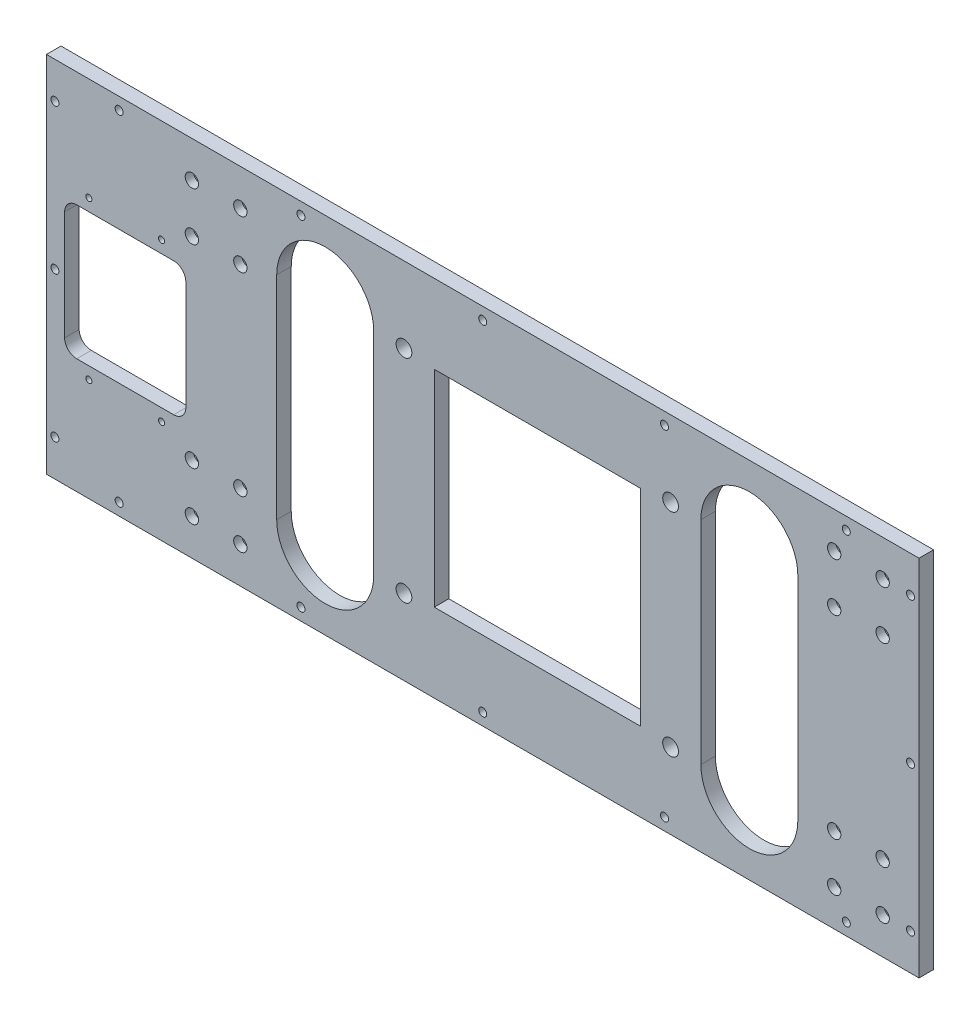
SolidWorks part; units mm, degrees
material "A3钢"
ref_plane "前视基准面" through (0, 0, 0) normal (0, 0, 1) x (1, 0, 0)
ref_plane "上视基准面" through (0, 0, 0) normal (0, 1, 0) x (1, 0, 0)
ref_plane "右视基准面" through (0, 0, 0) normal (1, 0, 0) x (0, 0, -1)
sketch "草图1" plane through (0, 0, 0) normal (0, 0, 1) x (1, 0, 0)
  line L1 (-360, -150) -> (360, -150)
  line L2 (-360, -150) -> (-360, 150)
  line L3 (-360, 150) -> (360, 150)
  line L4 (360, -150) -> (360, 150)
  line L5 (-360, -150) -> (360, 150) construction
  line L6 (-360, 150) -> (360, -150) construction
  point P0 (0, 0)
  dimension "D1" = 720
  dimension "D2" = 300
extrude "凸台-拉伸1" add sketch "草图1" along normal mid plane 12
sketch "草图2" plane through (0, 0, 6) normal (0, 0, 1) x (1, 0, 0)
  line L0 (45, 0) -> (235.2382, 0) construction
  line L1 (360, 150) -> (-360, 150) construction
  line L2 (-360, -150) -> (360, -150) construction
  line L3 (360, -150) -> (360, 150) construction
  circle A0 centre (45, 0) radius 30
  dimension "D1" = 60
  dimension "D2" = 315
extrude "切除-拉伸1" cut sketch "草图2" against normal through all
sketch "草图5" plane through (0, 0, 6) normal (0, 0, 1) x (1, 0, 0)
  line L0 (-45, 0) -> (45, 0) construction
  line L1 (45, 34.9467) -> (45, 0) construction
  circle A0 centre (-130, 87.5) radius 22.5
  circle A1 centre (-130, -87.5) radius 22.5
  circle A2 centre (220, -87.5) radius 22.5
  circle A3 centre (220, 87.5) radius 22.5
  dimension "D1" = 350
  dimension "D2" = 175
  dimension "D3" = 45
extrude "切除-拉伸2" cut sketch "草图5" against normal through all
hole_wizard "M6 螺纹孔1" positions "草图6" profile "草图7" tap size "M6" standard "GB" end condition through all
sketch "草图6" plane through (0, 0, 6) normal (0, 0, 1) x (1, 0, 0)
  line L0 (-243.226, 0) -> (45, 0) construction
  line L3 (45, 139.8405) -> (45, 0) construction
  line L4 (-130, 87.5) -> (-229.3436, 87.5) construction
  line L7 (-130, 87.5) -> (-130, 125.6853) construction
  circle A0 centre (45, 0) radius 30 construction
  point P117 (-154.5, 105)
  point P132 (-105.5, 105)
  point P133 (-105.5, 70)
  point P134 (-154.5, 70)
  point P135 (244.5, 70)
  point P136 (195.5, 70)
  point P137 (195.5, 105)
  point P138 (244.5, 105)
  point P139 (244.5, -105)
  point P140 (195.5, -105)
  point P141 (195.5, -70)
  point P142 (244.5, -70)
  point P143 (-154.5, -70)
  point P144 (-105.5, -70)
  point P145 (-105.5, -105)
  point P146 (-154.5, -105)
  dimension "D1" = 49
  dimension "D2" = 35
sketch "草图7" plane through (-154.5, -105, 6) normal (1, 0, 0) x (0, -1, 0)
  line L0 (0, 0) -> (0, 12)
  line L1 (0, 12) -> (2.5, 12)
  line L2 (2.5, 12) -> (2.5, 0)
  line L5 (2.5, 0) -> (0, 0)
  line L11 (0, -6.35) -> (0, 107.95) construction
  dimension "通孔螺纹孔钻头直径" = 5
  dimension "通孔螺纹孔钻头深度" = 12
cosmetic thread "孔螺蚊线1" parameters "D2"=6
cosmetic thread "孔螺蚊线2" parameters "D2"=6
cosmetic thread "孔螺蚊线3" parameters "D2"=6
cosmetic thread "孔螺蚊线4" parameters "D2"=6
cosmetic thread "孔螺蚊线5" parameters "D2"=6
cosmetic thread "孔螺蚊线6" parameters "D2"=6
cosmetic thread "孔螺蚊线7" parameters "D2"=6
cosmetic thread "孔螺蚊线8" parameters "D2"=6
cosmetic thread "孔螺蚊线9" parameters "D2"=6
cosmetic thread "孔螺蚊线10" parameters "D2"=6
cosmetic thread "孔螺蚊线11" parameters "D2"=6
cosmetic thread "孔螺蚊线12" parameters "D2"=6
cosmetic thread "孔螺蚊线13" parameters "D2"=6
cosmetic thread "孔螺蚊线14" parameters "D2"=6
cosmetic thread "孔螺蚊线15" parameters "D2"=6
cosmetic thread "孔螺蚊线16" parameters "D2"=6
hole_wizard "Ø13.0 (13) 直径孔1" positions "草图15" profile "草图16" hole size "Ø13.0" standard "GB" end condition through all
sketch "草图15" plane through (0, 0, 6) normal (0, 0, 1) x (1, 0, 0)
  line L0 (-244.6825, 0) -> (45, 0) construction
  line L3 (45, 139.2576) -> (45, -142.8825) construction
  circle A0 centre (45, 0) radius 30 construction
  point P0 (-65, 87.5)
  point P15 (155, 87.5)
  point P16 (155, -87.5)
  point P17 (-65, -87.5)
  dimension "D1" = 220
  dimension "D2" = 175
sketch "草图16" plane through (-65, 87.5, 6) normal (1, 0, 0) x (0, -1, 0)
  line L0 (0, 0) -> (0, 12)
  line L1 (0, 12) -> (6.5, 12)
  line L2 (6.5, 12) -> (6.5, 0)
  line L5 (6.5, 0) -> (0, 0)
  line L11 (0, -6.35) -> (0, 107.95) construction
  dimension "通孔孔直径" = 13
  dimension "通孔孔深度" = 12
sketch "草图17" plane through (0, 0, 6) normal (0, 0, 1) x (1, 0, 0)
  line L0 (-152.5, 87.5) -> (-107.5, 87.5) construction
  line L2 (225, -87.5) -> (-225, -87.5)
  line L3 (225, -87.5) -> (225, 87.5)
  line L4 (225, 87.5) -> (-225, 87.5)
  line L5 (-225, -87.5) -> (-225, 87.5)
  line L6 (225, -87.5) -> (-225, 87.5) construction
  line L7 (225, 87.5) -> (-225, -87.5) construction
  line L8 (-241, 102.5) -> (-209, 102.5)
  line L9 (-241, 102.5) -> (-241, 72.5)
  line L10 (-241, 72.5) -> (-209, 72.5)
  line L11 (-209, 102.5) -> (-209, 72.5)
  line L12 (-241, 102.5) -> (-209, 72.5) construction
  line L13 (-241, 72.5) -> (-209, 102.5) construction
  circle A0 centre (-130, 87.5) radius 22.5 construction
  point P5 (0, 0)
  dimension "D1" = 32
  dimension "D2" = 30
  dimension "D3" = 450
ref_plane "基准面1" through (0, 0, 0) normal (0, -1, 0) x (-1, 0, 0)
ref_plane "基准面2" through (0, 0, 0) normal (-1, 0, 0) x (0, 0, 1)
sketch "草图18" plane through (0, 0, 6) normal (0, 0, 1) x (1, 0, 0)
  line L0 (45, 0) -> (606.8786, 0) construction
  line L1 (310, -100) -> (-220, -100)
  line L2 (310, -100) -> (310, 100)
  line L3 (310, 100) -> (-220, 100)
  line L4 (-220, -100) -> (-220, 100)
  line L5 (310, -100) -> (-220, 100) construction
  line L6 (310, 100) -> (-220, -100) construction
  line L7 (45, 0) -> (45, 422.5031) construction
  line L8 (330, -80) -> (290, -120) construction
  line L9 (-240, 120) -> (-200, 120)
  line L10 (-240, 120) -> (-240, 80)
  line L11 (-240, 80) -> (-200, 80)
  line L12 (-200, 120) -> (-200, 80)
  line L13 (-240, 120) -> (-200, 80) construction
  line L14 (-240, 80) -> (-200, 120) construction
  line L15 (-240, -120) -> (-200, -120)
  line L16 (-240, -120) -> (-240, -80)
  line L17 (-240, -80) -> (-200, -80)
  line L18 (-200, -120) -> (-200, -80)
  line L19 (-240, -120) -> (-200, -80) construction
  line L20 (-240, -80) -> (-200, -120) construction
  line L21 (330, -120) -> (290, -80) construction
  line L22 (330, 80) -> (290, 120) construction
  line L23 (330, 120) -> (290, 80) construction
  line L24 (290, -120) -> (290, -80)
  line L25 (330, -80) -> (290, -80)
  line L26 (330, -120) -> (330, -80)
  line L27 (330, -120) -> (290, -120)
  line L28 (290, 120) -> (290, 80)
  line L29 (330, 80) -> (290, 80)
  line L30 (330, 120) -> (330, 80)
  line L31 (330, 120) -> (290, 120)
  line L32 (310, -100) -> (310, 100)
  line L33 (360, -150) -> (360, 150) construction
  line L34 (360, 150) -> (-360, 150) construction
  line L35 (-360, -150) -> (360, -150) construction
  dimension "D1" = 530
  dimension "D2" = 200
  dimension "D3" = 40
  dimension "D4" = 40
  dimension "D5" = 50
hole_wizard "打孔尺寸(%根据)内六角圆柱头螺钉的类型4" positions "3D草图1" profile "草图20" counterbore size "M6" standard "GB" end condition through all
sketch3d "3D草图1"
  point P0 (-240, 120, 6)
  point P3 (-200, 120, 6)
  point P6 (-200, 80, 6)
  point P9 (-240, 80, 6)
  point P12 (-200, -80, 6)
  point P15 (-200, -120, 6)
  point P18 (-240, -120, 6)
  point P21 (-240, -80, 6)
  point P25 (290, 120, 6)
  point P28 (330, 120, 6)
  point P31 (330, 80, 6)
  point P34 (290, 80, 6)
  point P37 (290, -80, 6)
  point P40 (330, -80, 6)
  point P43 (330, -120, 6)
  point P46 (290, -120, 6)
sketch "草图20" plane through (-240, 120, 6) normal (1, 0, 0) x (0, -1, 0)
  line L0 (0, 0) -> (0, 12)
  line L1 (0, 12) -> (3.3, 12)
  line L3 (3.3, 12) -> (3.3, 6.8)
  line L4 (3.3, 6.8) -> (5.5, 6.8)
  line L5 (5.5, 6.8) -> (5.5, 0)
  line L7 (5.5, 0) -> (0, 0)
  line L11 (0, -6.35) -> (0, 107.95) construction
  dimension "通孔孔直径" = 6.6
  dimension "通孔孔深度" = 12
  dimension "柱形沉头孔直径" = 11
  dimension "柱形沉头孔深度" = 6.8
sketch "草图21" plane through (0, 0, 6) normal (0, 0, 1) x (1, 0, 0)
  line L1 (-30, -75) -> (120, -75)
  line L2 (-30, -75) -> (-30, 75)
  line L3 (-30, 75) -> (120, 75)
  line L4 (120, -75) -> (120, 75)
  line L5 (-30, -75) -> (120, 75) construction
  line L6 (-30, 75) -> (120, -75) construction
  point P0 (45, 0)
  dimension "D1" = 150
sketch "草图22" plane through (0, 0, 6) normal (0, 0, 1) x (1, 0, 0)
  line L1 (-336.75, -24.75) -> (-287.25, -24.75)
  line L2 (-336.75, -24.75) -> (-336.75, 24.75)
  line L3 (-336.75, 24.75) -> (-287.25, 24.75)
  line L4 (-287.25, -24.75) -> (-287.25, 24.75)
  line L5 (-336.75, -24.75) -> (-287.25, 24.75) construction
  line L6 (-336.75, 24.75) -> (-287.25, -24.75) construction
  line L7 (0, 0) -> (-421.3567, 0) construction
  circle A1 centre (-240, 80) radius 3.3 construction
  point P0 (-312, 0)
  dimension "D1" = 72
  dimension "D2" = 49.5
  dimension "D3" = 49.5
sketch "草图26" plane through (0, 0, 6) normal (0, 0, 1) x (1, 0, 0)
  line L0 (45, 0) -> (485.4738, 0) construction
  line L1 (0.5, -44.5) -> (89.5, -44.5)
  line L2 (0.5, -44.5) -> (0.5, 44.5)
  line L3 (0.5, 44.5) -> (89.5, 44.5)
  line L4 (89.5, -44.5) -> (89.5, 44.5)
  line L5 (0.5, -44.5) -> (89.5, 44.5) construction
  line L6 (0.5, 44.5) -> (89.5, -44.5) construction
  line L7 (45, 0) -> (45, 266.8061) construction
  dimension "D1" = 89
  dimension "D2" = 89
hole_wizard "Ø11.0 (11) 直径孔1" positions "3D草图3" profile "草图27" hole size "Ø11.0" standard "GB" end condition through all
sketch3d "3D草图3"
  point P0 (-30, 75, 6)
  point P3 (122.598, 78.1933, 6)
  point P6 (-30, -75, 6)
  point P9 (120, -75, 6)
sketch "草图27" plane through (-30, 75, 6) normal (1, 0, 0) x (0, -1, 0)
  line L0 (0, 0) -> (0, 12)
  line L1 (0, 12) -> (5.5, 12)
  line L2 (5.5, 12) -> (5.5, 0)
  line L5 (5.5, 0) -> (0, 0)
  line L11 (0, -6.35) -> (0, 107.95) construction
  dimension "通孔孔直径" = 11
  dimension "通孔孔深度" = 12
hole_wizard "Ø11.0 (11) 直径孔2" positions "3D草图4" profile "草图28" hole size "Ø11.0" standard "GB" end condition through all
sketch3d "3D草图4"
  point P0 (0.5, -44.5, 6)
  point P3 (89.5, -44.5, 6)
  point P6 (89.5, 44.5, 6)
  point P9 (0.5, 44.5, 6)
sketch "草图28" plane through (0.5, -44.5, 6) normal (1, 0, 0) x (0, -1, 0)
  line L0 (0, 0) -> (0, 12)
  line L1 (0, 12) -> (5.5, 12)
  line L2 (5.5, 12) -> (5.5, 0)
  line L5 (5.5, 0) -> (0, 0)
  line L11 (0, -6.35) -> (0, 107.95) construction
  dimension "通孔孔直径" = 11
  dimension "通孔孔深度" = 12
sketch "草图29" plane through (0, 0, 6) normal (0, 0, 1) x (1, 0, 0)
  line L1 (-40, -85) -> (130, -85)
  line L2 (-40, -85) -> (-40, 85)
  line L3 (-40, 85) -> (130, 85)
  line L4 (130, -85) -> (130, 85)
  line L5 (-40, -85) -> (130, 85) construction
  line L6 (-40, 85) -> (130, -85) construction
  point P0 (45, 0)
  dimension "D1" = 170
extrude "切除-拉伸5" cut sketch "草图29" against normal through all
sketch "草图30" plane through (0, 0, 6) normal (0, 0, 1) x (1, 0, 0)
  line L0 (-130, 87.5) -> (-130, -87.5) construction
  line L1 (-90, 87.5) -> (-90, -87.5)
  line L2 (-170, 87.5) -> (-170, -87.5)
  line L3 (220, 87.5) -> (220, -87.5) construction
  line L4 (260, 87.5) -> (260, -87.5)
  line L5 (180, 87.5) -> (180, -87.5)
  arc A0 (-90, 87.5) -> (-170, 87.5) centre (-130, 87.5) ccw
  arc A1 (-170, -87.5) -> (-90, -87.5) centre (-130, -87.5) ccw
  arc A2 (260, 87.5) -> (180, 87.5) centre (220, 87.5) ccw
  arc A3 (180, -87.5) -> (260, -87.5) centre (220, -87.5) ccw
  point P2 (-130, 0)
  point P13 (220, 0)
  dimension "D1" = 40
extrude "切除-拉伸6" cut sketch "草图30" against normal through all
hole_wizard "M5 螺纹孔3" positions "3D草图5" profile "草图31" tap size "M5" standard "GB" end condition through all
sketch3d "3D草图5"
  point P0 (-336.75, 24.75, 6)
  point P3 (-287.25, 24.75, 6)
  point P6 (-287.25, -24.75, 6)
  point P9 (-336.75, -24.75, 6)
sketch "草图31" plane through (-336.75, 24.75, 6) normal (1, 0, 0) x (0, -1, 0)
  line L0 (0, 0) -> (0, 12)
  line L1 (0, 12) -> (2.1, 12)
  line L2 (2.1, 12) -> (2.1, 0)
  line L5 (2.1, 0) -> (0, 0)
  line L11 (0, -6.35) -> (0, 107.95) construction
  dimension "通孔螺纹孔钻头直径" = 4.2
  dimension "通孔螺纹孔钻头深度" = 12
cosmetic thread "孔螺蚊线29" parameters "D2"=5
cosmetic thread "孔螺蚊线30" parameters "D2"=5
cosmetic thread "孔螺蚊线31" parameters "D2"=5
cosmetic thread "孔螺蚊线32" parameters "D2"=5
sketch "草图32" plane through (0, 0, 6) normal (0, 0, 1) x (1, 0, 0)
  circle A0 centre (-312, 0) radius 28
  dimension "D1" = 56
extrude "切除-拉伸7" cut sketch "草图32" against normal through all
sketch "草图33" plane through (0, 0, -6) normal (0, 0, -1) x (-1, 0, 0)
  line L0 (360, 0) -> (-528.7833, 0) construction
  line L1 (360, 150) -> (360, -150) construction
  line L2 (0, -150) -> (0, 421.6194) construction
  line L3 (360, -150) -> (-360, -150) construction
  line L4 (353, -120) -> (353, 0) construction
  line L5 (353, 0) -> (353, 120) construction
  line L6 (-353, 0) -> (-353, 120) construction
  line L7 (-353, -120) -> (-353, 0) construction
  line L8 (300, -140) -> (150, -140) construction
  line L9 (150, -140) -> (0, -140) construction
  line L10 (0, -140) -> (-150, -140) construction
  line L11 (-150, -140) -> (-300, -140) construction
  line L12 (-150, 140) -> (-300, 140) construction
  line L13 (0, 140) -> (-150, 140) construction
  line L14 (150, 140) -> (0, 140) construction
  line L15 (300, 140) -> (150, 140) construction
  dimension "D1" = 7
  dimension "D2" = 120
  dimension "D3" = 140
  dimension "D4" = 150
hole_wizard "打孔尺寸(%根据)内六角圆柱头螺钉的类型4" positions "3D草图6" profile "草图34" counterbore size "M6" standard "GB" end condition through all
sketch3d "3D草图6"
  point P0 (-353, -120, -6)
  point P2 (-353, 0, -6)
  point P5 (-353, 120, -6)
  point P8 (-300, 140, -6)
  point P11 (-150, 140, -6)
  point P14 (0, 140, -6)
  point P17 (150, 140, -6)
  point P20 (300, 140, -6)
  point P23 (353, 120, -6)
  point P26 (353, 0, -6)
  point P29 (353, -120, -6)
  point P32 (300, -140, -6)
  point P35 (150, -140, -6)
  point P38 (0, -140, -6)
  point P41 (-150, -140, -6)
  point P45 (-300, -140, -6)
sketch "草图34" plane through (-353, -120, -6) normal (1, 0, 0) x (0, 1, 0)
  line L0 (0, 0) -> (0, 12)
  line L1 (0, 12) -> (3.3, 12)
  line L3 (3.3, 12) -> (3.3, 6.8)
  line L4 (3.3, 6.8) -> (5.5, 6.8)
  line L5 (5.5, 6.8) -> (5.5, 0)
  line L7 (5.5, 0) -> (0, 0)
  line L11 (0, -6.35) -> (0, 107.95) construction
  dimension "通孔孔直径" = 6.6
  dimension "通孔孔深度" = 12
  dimension "柱形沉头孔直径" = 11
  dimension "柱形沉头孔深度" = 6.8
sketch "草图35" plane through (0, 0, 6) normal (0, 0, 1) x (1, 0, 0)
  line L0 (-360, 0) -> (-139.2439, 0) construction
  line L1 (-341.8, -34.8) -> (-272.2, -34.8)
  line L2 (-341.8, -34.8) -> (-341.8, 34.8)
  line L3 (-341.8, 34.8) -> (-272.2, 34.8)
  line L4 (-272.2, -34.8) -> (-272.2, 34.8)
  line L5 (-341.8, -34.8) -> (-272.2, 34.8) construction
  line L6 (-341.8, 34.8) -> (-272.2, -34.8) construction
  line L7 (-360, 150) -> (-360, -150) construction
  point P0 (-307, 0)
  dimension "D1" = 69.6
  dimension "D2" = 69.6
  dimension "D3" = 53
hole_wizard "M6 螺纹孔2" positions "3D草图7" profile "草图37" tap size "M6" standard "GB" end condition through all
sketch3d "3D草图7"
  point P0 (-341.8, 34.8, 6)
  point P3 (-272.2, 34.8, 6)
  point P6 (-272.2, -34.8, 6)
  point P9 (-341.8, -34.8, 6)
sketch "草图37" plane through (-341.8, 34.8, 6) normal (1, 0, 0) x (0, -1, 0)
  line L0 (0, 0) -> (0, 12)
  line L1 (0, 12) -> (2.5, 12)
  line L2 (2.5, 12) -> (2.5, 0)
  line L5 (2.5, 0) -> (0, 0)
  line L11 (0, -6.35) -> (0, 107.95) construction
  dimension "通孔螺纹孔钻头直径" = 5
  dimension "通孔螺纹孔钻头深度" = 12
cosmetic thread "孔螺蚊线33" parameters "D2"=6
cosmetic thread "孔螺蚊线34" parameters "D2"=6
cosmetic thread "孔螺蚊线35" parameters "D2"=6
cosmetic thread "孔螺蚊线36" parameters "D2"=6
sketch "草图38" plane through (0, 0, 6) normal (0, 0, 1) x (1, 0, 0)
  line L0 (-360, 0) -> (-237.9477, 0) construction
  line L1 (-360, 150) -> (-360, -150) construction
  line L3 (-345, 55) -> (-245, 55)
  line L4 (-345, 55) -> (-345, -55)
  line L5 (-345, -55) -> (-245, -55)
  line L6 (-245, 55) -> (-245, -55)
  line L7 (-345, 55) -> (-245, -55) construction
  line L8 (-345, -55) -> (-245, 55) construction
  point P5 (-295, 0)
  dimension "D1" = 15
  dimension "D2" = 100
  dimension "D3" = 110
extrude "切除-拉伸8" cut sketch "草图38" against normal through all
sketch "草图39" plane through (0, 0, 6) normal (0, 0, 1) x (1, 0, 0)
  line L1 (-360, 0) -> (-127.0333, 0) construction
  line L2 (-360, 150) -> (-360, -150) construction
  line L3 (-325, -65) -> (-265, -65)
  line L4 (-325, -65) -> (-325, 65)
  line L5 (-325, 65) -> (-265, 65)
  line L6 (-265, -65) -> (-265, 65)
  line L7 (-325, -65) -> (-265, 65) construction
  line L8 (-325, 65) -> (-265, -65) construction
  point P0 (-295, 0)
  dimension "D1" = 35
  dimension "D2" = 60
  dimension "D3" = 130
hole_wizard "M6 螺纹孔3" positions "3D草图8" profile "草图40" tap size "M6" standard "GB" end condition through all
sketch3d "3D草图8"
  point P0 (-325, 65, 6)
  point P3 (-265, 65, 6)
  point P6 (-265, -65, 6)
  point P9 (-325, -65, 6)
sketch "草图40" plane through (-325, 65, 6) normal (1, 0, 0) x (0, -1, 0)
  line L0 (0, 0) -> (0, 12)
  line L1 (0, 12) -> (2.5, 12)
  line L2 (2.5, 12) -> (2.5, 0)
  line L5 (2.5, 0) -> (0, 0)
  line L11 (0, -6.35) -> (0, 107.95) construction
  dimension "通孔螺纹孔钻头直径" = 5
  dimension "通孔螺纹孔钻头深度" = 12
cosmetic thread "孔螺蚊线37" parameters "D2"=6
cosmetic thread "孔螺蚊线38" parameters "D2"=6
cosmetic thread "孔螺蚊线39" parameters "D2"=6
cosmetic thread "孔螺蚊线40" parameters "D2"=6
fillet "圆角1" radius 10 4 edges at (-345, 55, 0) (-245, 55, 0) (-245, -55, 0) (-345, -55, 0)
